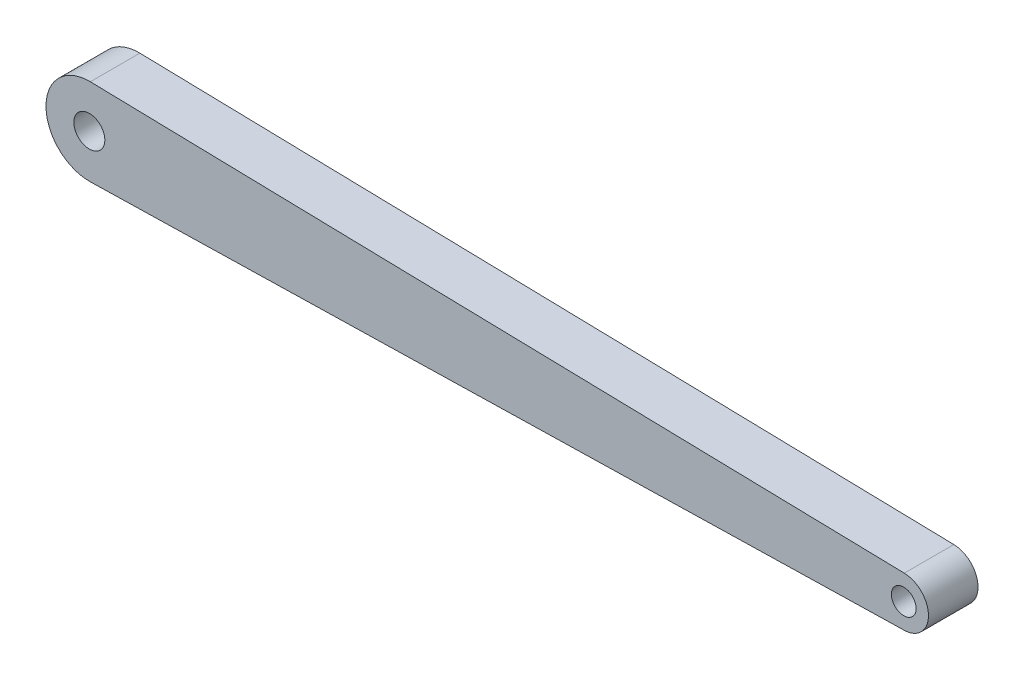
SolidWorks part; units mm, degrees
ref_plane "Front Plane" through (0, 0, 0) normal (0, 0, 1) x (1, 0, 0)
ref_plane "Top Plane" through (0, 0, 0) normal (0, 1, 0) x (1, 0, 0)
ref_plane "Right Plane" through (0, 0, 0) normal (1, 0, 0) x (0, 0, -1)
sketch "Sketch1" plane through (0, 0, 0) normal (0, 0, 1) x (1, 0, 0)
  line L0 (-1315, 0) -> (0, 0) construction
  line L1 (-1313.403, 69.9818) -> (0.9125, 39.9896)
  line L2 (0.9125, -39.9896) -> (-1313.403, -69.9818)
  circle A0 centre (0, 0) radius 20
  circle A1 centre (-1315, 0) radius 25
  arc A2 (-1313.403, 69.9818) -> (-1313.403, -69.9818) centre (-1315, 0) ccw
  arc A3 (0.9125, 39.9896) -> (0.9125, -39.9896) centre (0, 0) cw
  dimension "D1" = 40
  dimension "D2" = 50
  dimension "D3" = 1315
  dimension "D4" = 70
  dimension "D5" = 40
extrude "Boss-Extrude1" add sketch "Sketch1" along normal mid plane 80
